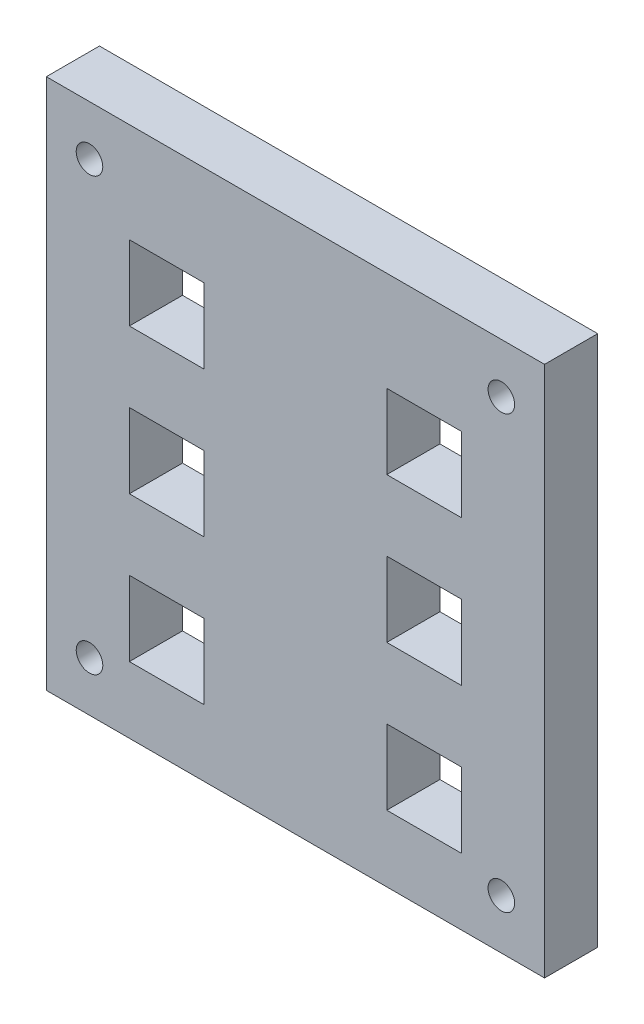
SolidWorks part; units mm, degrees
ref_plane "Front Plane" through (0, 0, 0) normal (0, 0, 1) x (1, 0, 0)
ref_plane "Top Plane" through (0, 0, 0) normal (0, 1, 0) x (1, 0, 0)
ref_plane "Right Plane" through (0, 0, 0) normal (1, 0, 0) x (0, 0, -1)
sketch "Sketch1" plane through (0, 0, 0) normal (0, 0, 1) x (1, 0, 0)
  line L0 (0, 0) -> (0, 64984.0187) construction
  line L1 (0, 0) -> (-64984.0187, 0) construction
  line L3 (75, -80) -> (-75, -80)
  line L4 (75, -80) -> (75, 80)
  line L5 (75, 80) -> (-75, 80)
  line L6 (-75, -80) -> (-75, 80)
  line L7 (75, -80) -> (-75, 80) construction
  line L8 (75, 80) -> (-75, -80) construction
  point P5 (0, 0)
  dimension "D1" = 150
  dimension "D2" = 160
extrude "Boss-Extrude1" add sketch "Sketch1" along normal blind 16
sketch "Sketch4" plane through (0, 0, 16) normal (0, 0, 1) x (1, 0, 0)
  line L0 (0, 0) -> (0, 50000) construction
  line L1 (0, 0) -> (-50000, 0) construction
  line L2 (75, 80) -> (-75, 80) construction
  line L3 (-50, 50) -> (-27.5, 50)
  line L4 (-50, 50) -> (-50, 27.5)
  line L5 (-50, 27.5) -> (-27.5, 27.5)
  line L6 (-27.5, 50) -> (-27.5, 27.5)
  line L7 (-75, 80) -> (-75, -80) construction
  line L8 (27.5, 50) -> (27.5, 27.5)
  line L9 (50, 27.5) -> (27.5, 27.5)
  line L10 (50, 50) -> (50, 27.5)
  line L11 (50, 50) -> (27.5, 50)
  line L12 (-75, -80) -> (75, -80) construction
  line L13 (-50, -60) -> (-27.5, -60)
  line L14 (-50, -60) -> (-50, -37.5)
  line L15 (-50, -37.5) -> (-27.5, -37.5)
  line L16 (-27.5, -60) -> (-27.5, -37.5)
  line L17 (27.5, -60) -> (27.5, -37.5)
  line L18 (50, -37.5) -> (27.5, -37.5)
  line L19 (50, -60) -> (50, -37.5)
  line L20 (50, -60) -> (27.5, -60)
  line L29 (27.5, 6.25) -> (50, -16.25) construction
  line L30 (-27.5, -16.25) -> (-50, -16.25)
  line L31 (-27.5, -16.25) -> (-27.5, 6.25)
  line L32 (-27.5, 6.25) -> (-50, 6.25)
  line L33 (-50, -16.25) -> (-50, 6.25)
  line L34 (-27.5, -16.25) -> (-50, 6.25) construction
  line L35 (-27.5, 6.25) -> (-50, -16.25) construction
  line L36 (27.5, -16.25) -> (50, 6.25) construction
  line L37 (50, -16.25) -> (50, 6.25)
  line L38 (27.5, 6.25) -> (50, 6.25)
  line L39 (27.5, -16.25) -> (27.5, 6.25)
  line L40 (27.5, -16.25) -> (50, -16.25)
  circle A0 centre (-62, 65) radius 4
  circle A1 centre (62, 65) radius 4
  circle A2 centre (62, -65) radius 4
  circle A3 centre (-62, -65) radius 4
  point P27 (-38.75, -5)
  point P32 (-38.75, 27.5)
  point P46 (38.75, -5)
  dimension "D9" = 8
  dimension "D1" = 22.5
  dimension "D2" = 22.5
  dimension "D3" = 30
  dimension "D4" = 25
  dimension "D5" = 22.5
  dimension "D6" = 22.5
  dimension "D7" = 20
  dimension "D8" = 25
  dimension "D10" = 22.5
  dimension "D11" = 65
  dimension "D12" = 62
  dimension "D13" = 22.5
  dimension "D14" = 32.5
  dimension "D15" = 25
extrude "Cut-Extrude1" cut sketch "Sketch4" against normal through all
